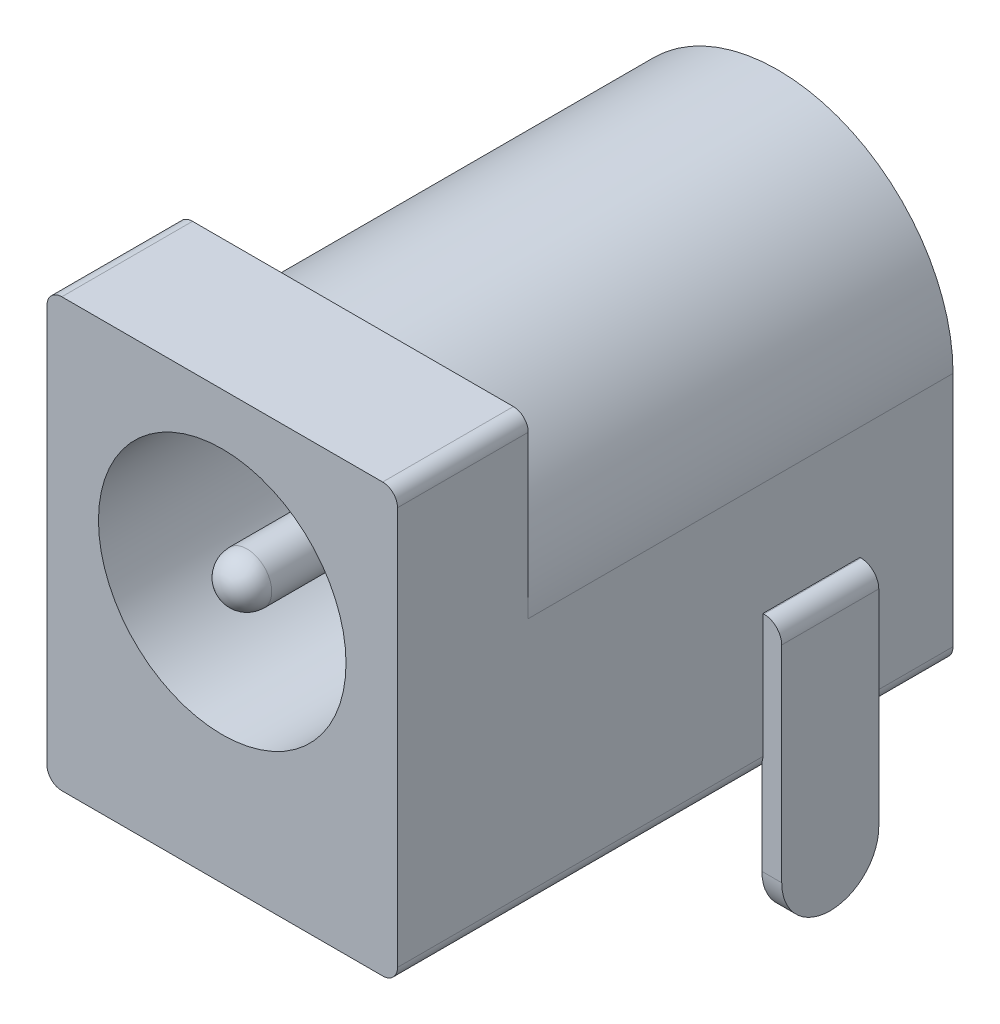
SolidWorks part; units mm, degrees
ref_plane "Front" through (0, 0, 0) normal (0, 0, 1) x (1, 0, 0)
ref_plane "Side" through (0, 0, 0) normal (0, 1, 0) x (1, 0, 0)
ref_plane "Top" through (0, 0, 0) normal (1, 0, 0) x (0, 0, -1)
sketch "Sketch1" plane through (0, 0, 0) normal (0, 0, 1) x (1, 0, 0)
  line L0 (0.381, 0) -> (8.6106, 0)
  line L1 (0, 0.381) -> (0, 10.5918)
  line L2 (8.6106, 10.9728) -> (0.381, 10.9728)
  line L3 (8.9916, 10.5918) -> (8.9916, 0.381)
  arc A0 (0.381, 10.9728) -> (0, 10.5918) centre (0.381, 10.5918) ccw
  arc A1 (8.9916, 10.5918) -> (8.6106, 10.9728) centre (8.6106, 10.5918) ccw
  arc A2 (8.6106, 0) -> (8.9916, 0.381) centre (8.6106, 0.381) ccw
  arc A3 (0.381, 0) -> (0, 0.381) centre (0.381, 0.381) cw
  point P13 (0, 0)
  dimension "D3" = 0.381
  dimension "D1" = 8.9916
  dimension "D2" = 10.9728
extrude "Base-Extrude" add sketch "Sketch1" along normal blind 14.2494
sketch "Sketch2" plane through (0, 0, 14.2494) normal (0, 0, 1) x (1, 0, 0)
  line L0 (0.381, 0) -> (8.6106, 0) construction
  line L1 (0, 0.381) -> (0, 10.5918) construction
  circle A0 centre (4.4958, 6.477) radius 3.175
  circle A1 centre (4.4958, 6.477) radius 0.635
  dimension "D1" = 6.477
  dimension "D2" = 4.4958
  dimension "D3" = 6.35
  dimension "D4" = 1.27
extrude "Cut-Extrude1" cut sketch "Sketch2" against normal blind 11.7094
fillet "Fillet1" radius 0.635 1 edges at (5.1308, 6.477, 14.2494)
sketch "Sketch3" plane through (0, 0, 0) normal (0, 0, -1) x (-1, 0, 0)
  line L4 (-0.381, 10.9728) -> (-8.6106, 10.9728)
  line L5 (-8.9916, 10.5918) -> (-8.9916, 0.381)
  line L6 (-8.6106, 0) -> (-0.381, 0)
  line L7 (0, 0.381) -> (0, 10.5918)
  line L8 (-0.381, 10.9728) -> (-8.6106, 10.9728)
  line L9 (-8.9916, 10.5918) -> (-8.9916, 6.4516)
  line L11 (0, 6.4516) -> (0, 10.5918)
  arc A0 (0, 6.4516) -> (-8.9916, 6.4516) centre (-4.4958, 6.4516) ccw
  arc A5 (0, 10.5918) -> (-0.381, 10.9728) centre (-0.381, 10.5918) ccw
  arc A6 (-8.6106, 10.9728) -> (-8.9916, 10.5918) centre (-8.6106, 10.5918) ccw
  arc A7 (-8.9916, 0.381) -> (-8.6106, 0) centre (-8.6106, 0.381) ccw
  arc A8 (-0.381, 0) -> (0, 0.381) centre (-0.381, 0.381) ccw
  arc A9 (0, 10.5918) -> (-0.381, 10.9728) centre (-0.381, 10.5918) ccw
  arc A10 (-8.6106, 10.9728) -> (-8.9916, 10.5918) centre (-8.6106, 10.5918) ccw
  dimension "D2" = 0.0254
  dimension "D1" = 0
extrude "Cut-Extrude2" cut sketch "Sketch3" against normal offset from surface (10.8966 mm away) 3.3528
sketch "Sketch4" plane through (0, 0, 0) normal (0, -1, 0) x (1, 0, 0)
  line L0 (8.9662, 2.3876) -> (9.4742, 2.3876)
  line L1 (8.9662, 2.3876) -> (8.9662, 4.8768)
  line L2 (9.4742, 4.8768) -> (8.9662, 4.8768)
  line L3 (9.4742, 4.8768) -> (9.4742, 2.3876)
  line L4 (2.9972, 0.381) -> (5.9944, 0.381)
  line L5 (2.9972, 0.381) -> (2.9972, 0.889)
  line L6 (5.9944, 0.889) -> (2.9972, 0.889)
  line L7 (5.9944, 0.889) -> (5.9944, 0.381)
  line L8 (3.2512, 6.7564) -> (5.7404, 6.7564)
  line L9 (3.2512, 6.7564) -> (3.2512, 7.0104)
  line L10 (5.7404, 7.0104) -> (3.2512, 7.0104)
  line L11 (5.7404, 7.0104) -> (5.7404, 6.7564)
  line L13 (4.4958, 0) -> (4.4958, 14.2494) construction
  line L14 (0.381, 0) -> (8.6106, 0) construction
  line L15 (0.381, 14.2494) -> (8.6106, 14.2494) construction
  line L17 (8.9916, 14.2494) -> (8.9916, 0) construction
  dimension "D1" = 0.508
  dimension "D2" = 2.9972
  dimension "D3" = 2.4892
  dimension "D4" = 2.4892
  dimension "D5" = 0.0254
  dimension "D6" = 0.508
  dimension "D7" = 1.2446
  dimension "D8" = 1.4986
  dimension "D9" = 7.239
  dimension "D10" = 0.254
  dimension "D11" = 6.6294
  dimension "D12" = 1.8796
extrude "Boss-Extrude1" add sketch "Sketch4" along normal blind 3.683 and the other way blind 3.556
fillet "Fillet2" radius 0.4572 1 edges at (9.4742, 3.556, 3.6322)
sketch "Sketch5" plane through (0, 0, 0.381) normal (0, 0, -1) x (-1, 0, 0)
  line L0 (-2.9972, -3.683) -> (-2.9972, 0) construction
  line L1 (-5.9944, -3.683) -> (-5.9944, 0) construction
  line L3 (-2.9972, -3.683) -> (-5.9944, -3.683) construction
  line L4 (-2.9972, -3.683) -> (-5.9944, -3.683)
  line L5 (-2.9972, -3.683) -> (-2.9972, -1.9304)
  line L6 (-5.9944, -3.683) -> (-5.9944, -1.9304)
  arc A0 (-5.9944, -1.9304) -> (-2.9972, -1.9304) centre (-4.4958, -1.9304) ccw
  dimension "D1" = 0.254
extrude "Cut-Extrude3" cut sketch "Sketch5" against normal blind 0.508
sketch "Sketch6" plane through (0.3123, -0.3541, 6.7564) normal (0, 0, -1) x (-1, 0, 0)
  line L2 (-5.4281, -3.3289) -> (-5.4281, 0.3541) construction
  line L4 (-2.9389, -3.3289) -> (-5.4281, -3.3289)
  line L5 (-2.9389, -3.3289) -> (-2.9389, -1.8303)
  line L6 (-5.4281, -3.3289) -> (-5.4281, -1.8303)
  line L7 (-2.9389, -3.3289) -> (-2.9389, 0.3541) construction
  line L10 (-2.9389, -3.3289) -> (-5.4281, -3.3289) construction
  arc A0 (-5.4281, -1.8303) -> (-2.9389, -1.8303) centre (-4.1835, -1.8303) ccw
  dimension "D1" = 0.254
extrude "Cut-Extrude4" cut sketch "Sketch6" against normal blind 0.508
sketch "Sketch7" plane through (9.4742, 0, 0) normal (1, 0, 0) x (0, 0, -1)
  line L0 (-2.3876, -3.683) -> (-2.3876, 3.0988) construction
  line L1 (-4.8768, -3.683) -> (-2.3876, -3.683) construction
  line L2 (-4.8768, -3.683) -> (-4.8768, 3.0988) construction
  line L3 (-2.3876, -3.683) -> (-2.3876, -2.1844)
  line L4 (-4.8768, -3.683) -> (-2.3876, -3.683)
  line L5 (-4.8768, -3.683) -> (-4.8768, -2.1844)
  arc A0 (-4.8768, -2.1844) -> (-2.3876, -2.1844) centre (-3.6322, -2.1844) ccw
  dimension "D1" = 0.254
extrude "Cut-Extrude5" cut sketch "Sketch7" against normal blind 0.508
sketch "Sketch8" plane through (0, 0, 0) normal (0, 1, 0) x (1, 0, 0)
  line L0 (4.4958, -0.381) -> (4.4958, -0.635) construction
  line L1 (2.9972, -0.381) -> (5.9944, -0.381) construction
  line L2 (5.9944, -0.635) -> (4.4958, -0.635) construction
  line L3 (5.9944, -0.889) -> (5.9944, -0.381) construction
  line L4 (9.2456, -2.3876) -> (9.2456, -3.6322) construction
  line L5 (9.4742, -2.3876) -> (9.017, -2.3876) construction
  line L6 (9.4742, -3.6322) -> (9.2456, -3.6322) construction
  line L7 (9.4742, -2.3876) -> (9.4742, -4.8768) construction
  line L8 (4.4958, -6.7564) -> (4.4958, -6.8834) construction
  line L9 (3.2515, -6.7564) -> (5.7401, -6.7564) construction
  line L10 (3.2515, -6.8834) -> (4.4958, -6.8834) construction
  line L11 (3.2515, -6.7564) -> (3.2515, -7.0104) construction
  circle A0 centre (4.4958, -0.635) radius 1.778
  circle A1 centre (9.2456, -3.6322) radius 1.524
  circle A2 centre (4.4958, -6.8834) radius 1.524
  dimension "D4" = 3.556
  dimension "D5" = 3.048
  dimension "D6" = 3.048
  dimension "D1" = 4.7498
  dimension "D2" = 3.2512
  dimension "D3" = 2.9972
sketch "Sketch9" plane through (0, 0, 14.2494) normal (0, 0, 1) x (1, 0, 0)
  line L8 (-0.508, 10.5918) -> (-0.508, 0.381)
  line L9 (0.381, -0.508) -> (8.6106, -0.508)
  line L10 (9.4996, 0.381) -> (9.4996, 10.5918)
  line L11 (8.6106, 11.4808) -> (0.381, 11.4808)
  line L12 (-0.508, 10.5918) -> (-0.508, 0.381) construction
  line L13 (0.381, -0.508) -> (8.6106, -0.508) construction
  line L14 (9.4996, 0.381) -> (9.4996, 10.5918) construction
  line L15 (8.6106, 11.4808) -> (0.381, 11.4808) construction
  arc A8 (0.381, 11.4808) -> (-0.508, 10.5918) centre (0.381, 10.5918) ccw
  arc A9 (-0.508, 0.381) -> (0.381, -0.508) centre (0.381, 0.381) ccw
  arc A10 (8.6106, -0.508) -> (9.4996, 0.381) centre (8.6106, 0.381) ccw
  arc A11 (9.4996, 10.5918) -> (8.6106, 11.4808) centre (8.6106, 10.5918) ccw
  arc A12 (0.381, 11.4808) -> (-0.508, 10.5918) centre (0.381, 10.5918) ccw construction
  arc A13 (-0.508, 0.381) -> (0.381, -0.508) centre (0.381, 0.381) ccw construction
  arc A14 (8.6106, -0.508) -> (9.4996, 0.381) centre (8.6106, 0.381) ccw construction
  arc A15 (9.4996, 10.5918) -> (8.6106, 11.4808) centre (8.6106, 10.5918) ccw construction
  dimension "D1" = 0.508
